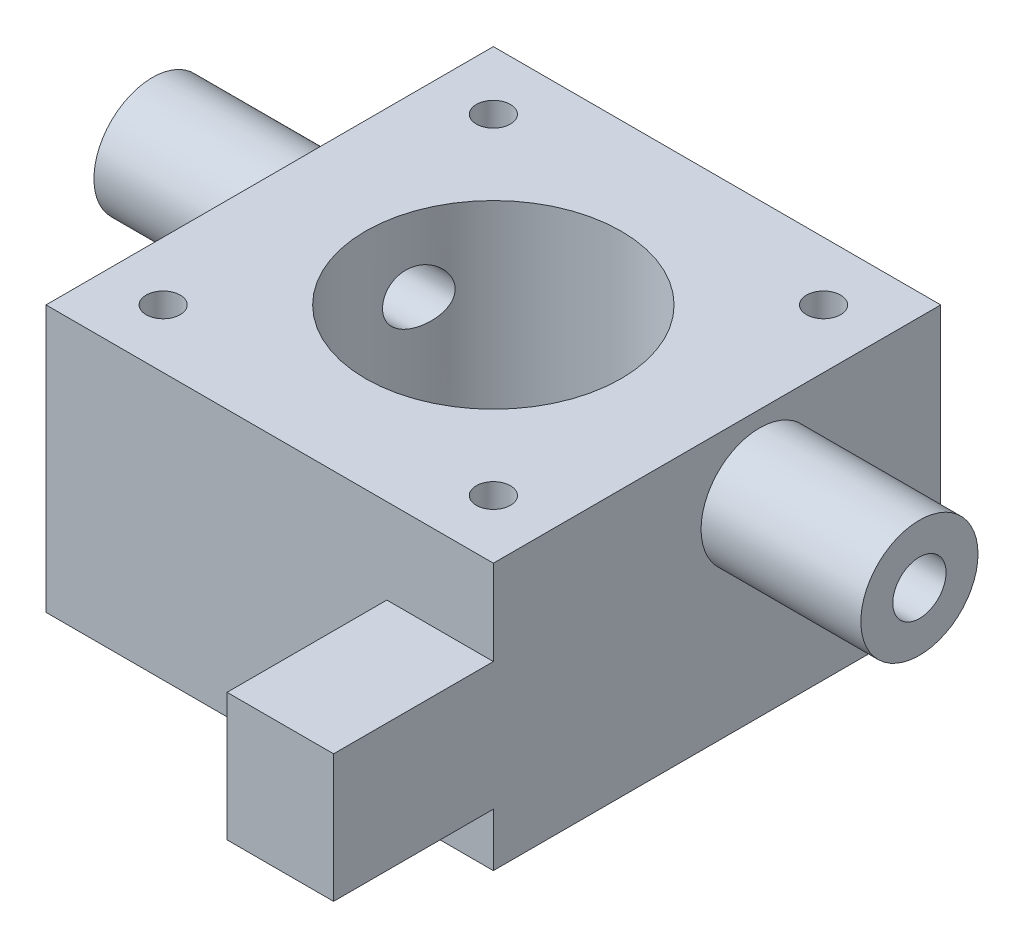
SolidWorks part; units mm, degrees
ref_plane "前视基准面" through (0, 0, 0) normal (0, 0, 1) x (1, 0, 0)
ref_plane "上视基准面" through (0, 0, 0) normal (0, 1, 0) x (1, 0, 0)
ref_plane "右视基准面" through (0, 0, 0) normal (1, 0, 0) x (0, 0, -1)
other "Configuration Table"
sketch "草图1" plane through (0, 0, 0) normal (0, 1, 0) x (1, 0, 0)
  line L1 (-21, 21) -> (21, 21)
  line L2 (-21, 21) -> (-21, -21)
  line L3 (-21, -21) -> (21, -21)
  line L4 (21, 21) -> (21, -21)
  line L5 (-21, 21) -> (21, -21) construction
  line L6 (-21, -21) -> (21, 21) construction
  point P0 (0, 0)
  dimension "D1" = 42
  dimension "D2" = 42
extrude "凸台-拉伸1" add sketch "草图1" along normal blind 25
sketch "草图2" plane through (0, 0, 21) normal (0, 0, 1) x (1, 0, 0)
  line L0 (21, 17) -> (11, 17)
  line L1 (21, 25) -> (21, 0) construction
  line L2 (11, 17) -> (11, 5)
  line L3 (11, 5) -> (21, 5)
  line L4 (21, 5) -> (21, 17)
  line L5 (-21, 0) -> (21, 0) construction
  dimension "D1" = 5
  dimension "D2" = 12
  dimension "D3" = 10
extrude "凸台-拉伸2" add sketch "草图2" along normal blind 15
sketch "草图3" plane through (21, 0, 0) normal (1, 0, 0) x (0, 0, -1)
  line L0 (-21, 25) -> (-21, 17) construction
  line L1 (-21, 0) -> (21, 0) construction
  circle A0 centre (4, 18) radius 5.5
  dimension "D1" = 25
  dimension "D2" = 11
  dimension "D3" = 18
extrude "凸台-拉伸3" add sketch "草图3" along normal blind 15 and the other way offset from surface (57 mm away) 15 other way up to face at (-21, 12.5, 0)
sketch "草图4" plane through (36, 0, 0) normal (1, 0, 0) x (0, 0, -1)
  circle A2 centre (4, 18) radius 2.5
  circle A3 centre (4, 18) radius 2.5
  dimension "D1" = 3
extrude "切除-拉伸1" cut sketch "草图4" against normal up to next
sketch "草图5" plane through (0, 25, 0) normal (0, 1, 0) x (1, 0, 0)
  line L0 (-66.941, 0) -> (53.0685, 0) construction
  line L1 (0, 49.6837) -> (0, -35.9018) construction
  circle A0 centre (0, 0) radius 12
  circle A1 centre (-15.5, 15.5) radius 1.6
  circle A2 centre (15.5, 15.5) radius 1.6
  circle A3 centre (15.5, -15.5) radius 1.6
  circle A4 centre (-15.5, -15.5) radius 1.6
  dimension "D1" = 24
  dimension "D2" = 3.2
  dimension "D3" = 15.5
  dimension "D4" = 15.5
extrude "切除-拉伸2" cut sketch "草图5" against normal up to next
